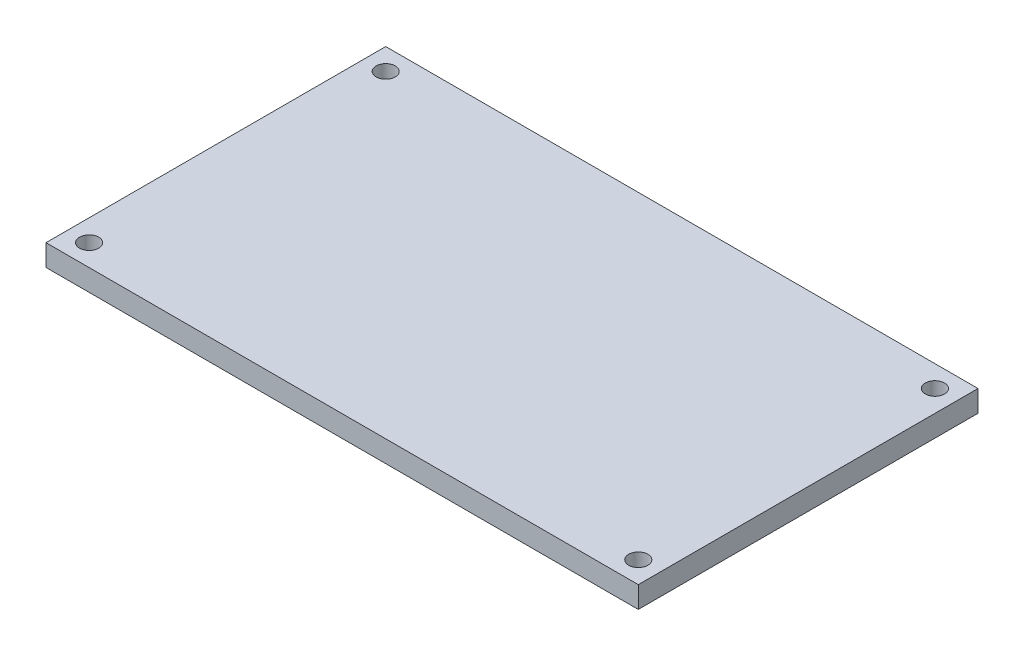
SolidWorks part; units mm, degrees
material "Maple"
ref_plane "Front Plane" through (0, 0, 0) normal (0, 0, 1) x (1, 0, 0)
ref_plane "Top Plane" through (0, 0, 0) normal (0, 1, 0) x (1, 0, 0)
ref_plane "Right Plane" through (0, 0, 0) normal (1, 0, 0) x (0, 0, -1)
sketch "Sketch1" plane through (0, 0, 0) normal (0, 1, 0) x (1, 0, 0)
  line L1 (-43.735, 25.085) -> (43.735, 25.085)
  line L2 (-43.735, 25.085) -> (-43.735, -25.085)
  line L3 (-43.735, -25.085) -> (43.735, -25.085)
  line L4 (43.735, 25.085) -> (43.735, -25.085)
  line L5 (-43.735, 25.085) -> (43.735, -25.085) construction
  line L6 (-43.735, -25.085) -> (43.735, 25.085) construction
  point P0 (0, 0)
  dimension "D1" = 87.47
  dimension "D2" = 50.17
extrude "Boss-Extrude1" add sketch "Sketch1" along normal blind 3.175
sketch "Sketch2" plane through (0, 3.175, 0) normal (0, 1, 0) x (1, 0, 0)
  line L0 (-43.735, -25.085) -> (-40.553, -21.903) construction
  line L1 (-43.735, -25.085) -> (43.735, -25.085) construction
  line L2 (0, 0) -> (0, -9.363) construction
  line L3 (0, 0) -> (-12.1021, 0) construction
  circle A0 centre (-40.553, -21.903) radius 1.415
  circle A1 centre (40.553, -21.903) radius 1.415
  circle A2 centre (40.553, 21.903) radius 1.415
  circle A3 centre (-40.553, 21.903) radius 1.415
  dimension "D3" = 2.83
  dimension "D1" = 45
  dimension "D2" = 4.5
extrude "Cut-Extrude1" cut sketch "Sketch2" against normal through all
equation "\"length\"=87.3"
equation "\"D1@Sketch1\"=\"length\" + 2*\"kerf\""
equation "\"width\"=50"
equation "\"D2@Sketch1\"=\"width\" + 2*\"kerf\""
equation "\"depth\"=3.175"
equation "\"D1@Boss-Extrude1\"=\"depth\""
equation "\"kerf\"= 0.17 / 2"
equation "\"D3@Sketch2\"=3 - 2*\"kerf\""
